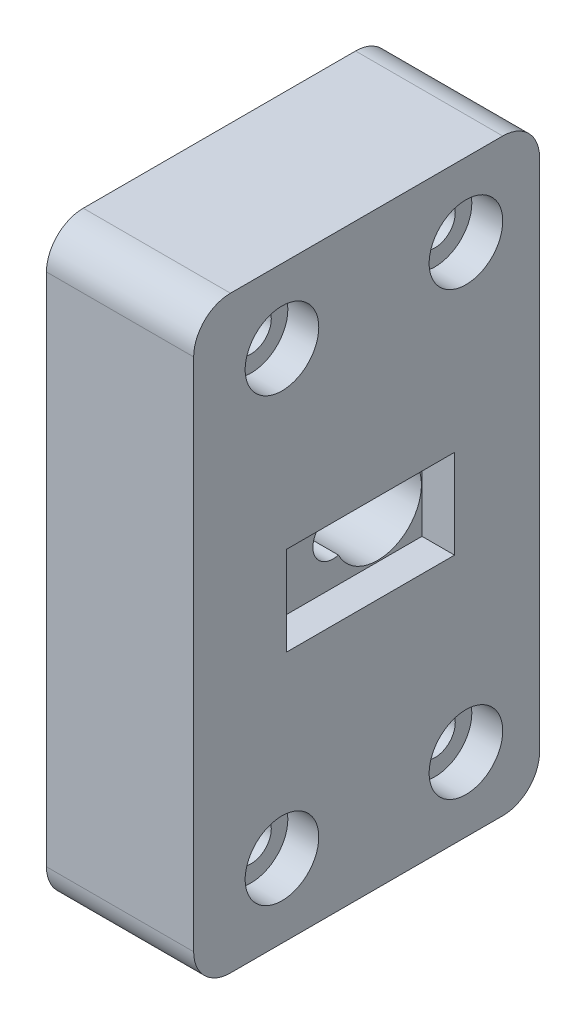
SolidWorks part; units mm, degrees
material "PMMA"
ref_plane "Plan de face" through (0, 0, 0) normal (0, 0, 1) x (1, 0, 0)
ref_plane "Plan de dessus" through (0, 0, 0) normal (0, 1, 0) x (1, 0, 0)
ref_plane "Plan de droite" through (0, 0, 0) normal (1, 0, 0) x (0, 0, -1)
sketch "Esquisse1" plane through (0, 0, 0) normal (0, 0, 1) x (1, 0, 0)
  line L0 (10, 57.5) -> (10, 80) construction
  line L1 (0, 0) -> (20, 0)
  line L2 (0, 0) -> (0, 80)
  line L3 (0, 80) -> (20, 80)
  line L4 (20, 0) -> (20, 80)
  line L5 (10, 22.5) -> (10, 0) construction
  dimension "D1" = 80
  dimension "D2" = 20
  dimension "D4" = 35
  dimension "D5" = 10
extrude "Boss.-Extru.1" add sketch "Esquisse1" along normal blind 47
sketch "Esquisse2" plane through (0, 0, 0) normal (-1, 0, 0) x (0, 0, 1)
  line L0 (47, 80) -> (47, 0) construction
  line L1 (0, 80) -> (0, 0) construction
  circle A0 centre (17.5, 40) radius 13.05
  point P9 (0, 40)
  dimension "D2" = 26.1
  dimension "D1" = 29.5
extrude "Enlèv. mat.-Extru.1" cut sketch "Esquisse2" against normal blind 8
sketch "Esquisse3" plane through (8, 0, 0) normal (-1, 0, 0) x (0, 0, 1)
  arc A0 (22.8258, 42.6529) -> (22.8258, 37.3471) centre (17.5, 40) ccw
  circle A1 centre (17.5, 40) radius 13.05 construction
  arc A2 (22.8258, 37.3471) -> (22.8258, 42.6529) centre (23.55, 40) ccw
  dimension "D1" = 11.9
  dimension "D2" = 5.5
  dimension "D3" = 6.05
extrude "Enlèv. mat.-Extru.2" cut sketch "Esquisse3" against normal up to next
hole_wizard "Chambrage pour vis à tête hexagonale M52" positions "Esquisse6" profile "Esquisse7" counterbore size "M5" standard "DIN" end condition through all
sketch "Esquisse6" plane through (20, 0, 0) normal (1, 0, 0) x (0, 0, -1)
  line L0 (0, 0) -> (0, 80) construction
  line L1 (-47, 0) -> (0, 0) construction
  point P0 (-10, 70)
  point P2 (-35, 70)
  point P4 (-35, 10)
  point P6 (-10, 10)
  dimension "D1" = 25
  dimension "D2" = 10
  dimension "D3" = 60
  dimension "D4" = 10
sketch "Esquisse7" plane through (20, 70, 10) normal (0, 1, 0) x (0, 0, -1)
  line L0 (0, 0) -> (0, 20)
  line L1 (0, 20) -> (2.75, 20)
  line L3 (2.75, 20) -> (2.75, 4.2)
  line L4 (2.75, 4.2) -> (5, 4.2)
  line L5 (5, 4.2) -> (5, 0)
  line L7 (5, 0) -> (0, 0)
  line L11 (0, -6.35) -> (0, 107.95) construction
  dimension "Diamètre du perçage jusqu'au prochain" = 5.5
  dimension "Profondeur du perçage jusqu'au prochain" = 20
  dimension "Diamètre du chambrage" = 10
  dimension "Profondeur du chambrage" = 4.2
fillet "Congé1" radius 5 4 edges at (10, 0, 47) (10, 80, 47) (10, 80, 0) (10, 0, 0)
ref_plane "Plan1" through (20, 0, 0) normal (1, 0, 0) x (0, 0, -1)
sketch "Esquisse8" plane through (20, 0, 0) normal (1, 0, 0) x (0, 0, -1)
  line L0 (8.1647, 40) -> (-55.0627, 40) construction
  line L1 (-11.55, 46.05) -> (-34.35, 46.05)
  line L2 (-11.55, 46.05) -> (-11.55, 33.95)
  line L3 (-11.55, 33.95) -> (-34.35, 33.95)
  line L4 (-34.35, 46.05) -> (-34.35, 33.95)
  line L5 (-42, 80) -> (-5, 80) construction
  line L6 (-42, 0) -> (-5, 0) construction
  circle A0 centre (-17.5, 40) radius 5.95 construction
  dimension "D1" = 12.1
  dimension "D2" = 22.8
extrude "Enlèv. mat.-Extru.4" cut sketch "Esquisse8" against normal blind 4.5 draft 1 draft outward yes
chamfer "Chanfrein1" distance 0.5 angle 45 1 edges at (0, 40, 30.55)
